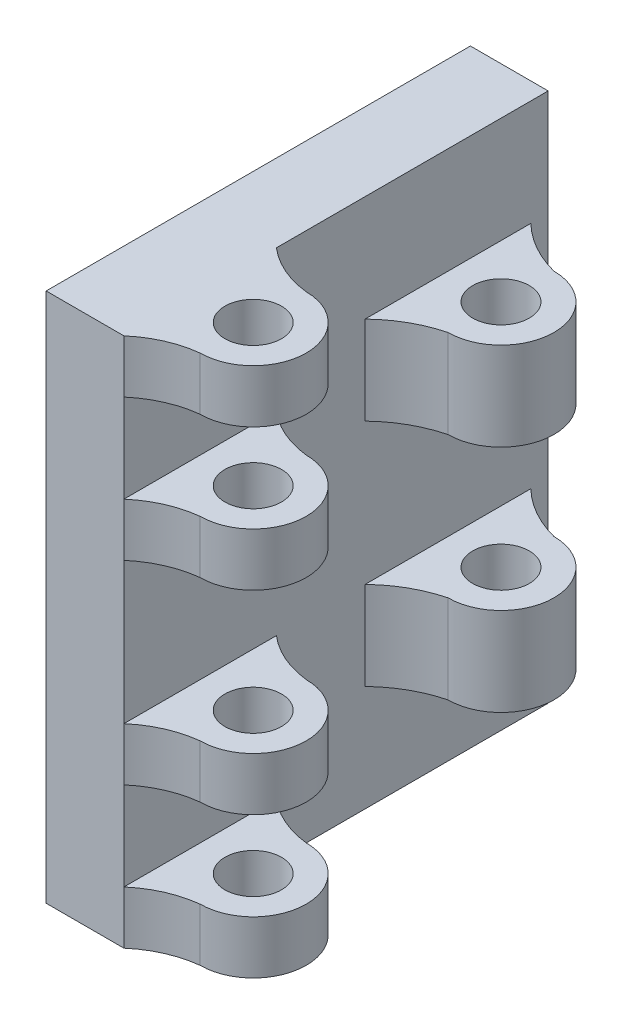
SolidWorks part; units mm, degrees
ref_plane "Płaszczyzna przednia" through (0, 0, 0) normal (0, 0, 1) x (1, 0, 0)
ref_plane "Płaszczyzna górna" through (0, 0, 0) normal (0, 1, 0) x (1, 0, 0)
ref_plane "Płaszczyzna prawa" through (0, 0, 0) normal (1, 0, 0) x (0, 0, -1)
sketch "Szkic2" plane through (0, 0, 0) normal (0, 1, 0) x (1, 0, 0)
  line L1 (-11, 60) -> (11, 60)
  line L2 (-11, 60) -> (-11, -60)
  line L3 (-11, -60) -> (11, -60)
  line L4 (11, 60) -> (11, -60)
  line L5 (-11, 60) -> (11, -60) construction
  line L6 (-11, -60) -> (11, 60) construction
  point P0 (0, 0)
  dimension "D1" = 120
  dimension "D2" = 22
extrude "Dodanie-wyciągnięcie1" add sketch "Szkic2" along normal blind 150
sketch "Szkic3" plane through (0, 0, 0) normal (0, 1, 0) x (1, 0, 0)
  line L0 (11, -60) -> (11, 60) construction
  line L10 (11, -16.8649) -> (11, -60)
  arc A0 (26, -53.4324) -> (26, -23.4324) centre (26, -38.4324) ccw
  arc A1 (26, -53.4324) -> (11, -60) centre (29.1283, -80.9907) ccw
  arc A2 (26, -23.4324) -> (11, -16.8649) centre (29.1283, 4.1258) cw
  circle A3 centre (26, -38.4324) radius 8
  dimension "D1" = 15
extrude "Dodanie-wyciągnięcie2" add sketch "Szkic3" along normal blind 15
pattern_linear "Szyk liniowy1" count 2 spacing 40 along (0, 1, 0) of "Dodanie-wyciągnięcie2"
pattern_linear "Szyk liniowy2" count 2 spacing 135 along (0, 1, 0) of "Dodanie-wyciągnięcie2"
pattern_linear "Szyk liniowy3" count 2 spacing 95 along (0, 1, 0) of "Dodanie-wyciągnięcie2"
ref_plane "Płaszczyzna1" through (0, 30, 0) normal (0, -1, 0) x (-1, 0, 0)
sketch "Szkic4" plane through (0, 30, 0) normal (0, -1, 0) x (-1, 0, 0)
  line L0 (-11, -16.8649) -> (-11, 60) construction
  line L1 (-11, 55.0958) -> (-11, 8.2163)
  arc A0 (-26, 46.656) -> (-26, 16.656) centre (-26, 31.656) ccw
  arc A1 (-26, 16.656) -> (-11, 8.2163) centre (-34.3723, -15.7738) cw
  arc A2 (-26, 46.656) -> (-11, 55.0958) centre (-34.3723, 79.0859) ccw
  circle A3 centre (-26, 31.656) radius 8
  dimension "D1" = 15
extrude "Dodanie-wyciągnięcie3" add sketch "Szkic4" against normal blind 25
pattern_linear "Szyk liniowy4" count 2 spacing 65 along (0, 1, 0) of "Dodanie-wyciągnięcie3"
